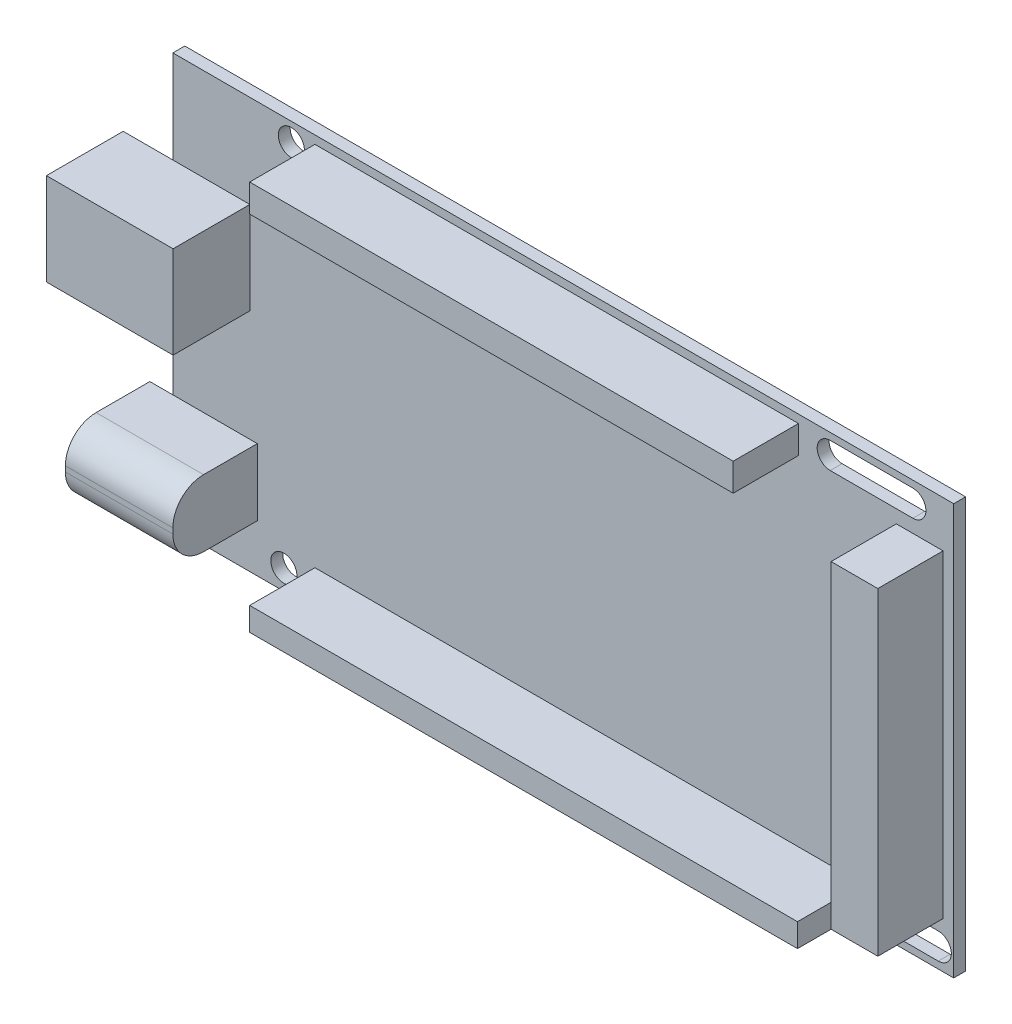
SolidWorks part; units mm, degrees
ref_plane "前视" through (0, 0, 0) normal (0, 0, 1) x (1, 0, 0)
ref_plane "上视" through (0, 0, 0) normal (0, 1, 0) x (1, 0, 0)
ref_plane "右视" through (0, 0, 0) normal (1, 0, 0) x (0, 0, -1)
sketch "草图1" plane through (0, 0, 0) normal (0, 0, 1) x (1, 0, 0)
  line L1 (-49.2002, 28.0388) -> (52.4998, 28.0388)
  line L2 (-49.2002, 28.0388) -> (-49.2002, -25.4612)
  line L3 (-49.2002, -25.4612) -> (52.4998, -25.4612)
  line L4 (52.4998, 28.0388) -> (52.4998, -25.4612)
extrude "凸台-拉伸1" add sketch "草图1" along normal blind 1.55
sketch "草图2" plane through (0, 0, 1.55) normal (0, 0, 1) x (1, 0, 0)
  line L0 (-49.2002, -25.4612) -> (52.4998, -25.4612) construction
  line L1 (-49.2002, 28.0388) -> (-49.2002, -25.4612) construction
  line L2 (52.4998, 28.0388) -> (-49.2002, 28.0388) construction
  line L3 (36.4187, 25.4388) -> (47.1808, 25.4388) construction
  line L4 (36.4187, 27.1388) -> (47.1808, 27.1388)
  line L5 (36.4187, 23.7388) -> (47.1808, 23.7388)
  line L6 (52.4998, -25.4612) -> (52.4998, 28.0388) construction
  line L7 (45.1092, -22.8612) -> (50.4903, -22.8612) construction
  line L8 (45.1092, -21.1612) -> (50.4903, -21.1612)
  line L9 (45.1092, -24.5612) -> (50.4903, -24.5612)
  circle A0 centre (-34.7402, -22.8612) radius 1.7
  circle A1 centre (-33.7702, 25.6388) radius 1.7
  arc A2 (36.4187, 27.1388) -> (36.4187, 23.7388) centre (36.4187, 25.4388) ccw
  arc A3 (47.1808, 23.7388) -> (47.1808, 27.1388) centre (47.1808, 25.4388) ccw
  arc A4 (45.1092, -21.1612) -> (45.1092, -24.5612) centre (45.1092, -22.8612) ccw
  arc A5 (50.4903, -24.5612) -> (50.4903, -21.1612) centre (50.4903, -22.8612) ccw
  point P12 (41.7998, 25.4388)
  point P21 (47.7998, -22.8612)
  dimension "D1" = 2.6
  dimension "D3" = 2.4
  dimension "D2" = 14.46
  dimension "D4" = 15.43
  dimension "D5" = 3.4
  dimension "D6" = 10.7622
  dimension "D7" = 2.6
  dimension "D8" = 10.7
  dimension "D9" = 3.4
  dimension "D10" = 5.3811
  dimension "D11" = 4.7
extrude "切除-拉伸1" cut sketch "草图2" against normal blind 1.55
sketch "草图3" plane through (0, 0, 1.55) normal (0, 0, 1) x (1, 0, 0)
  line L0 (-55.6702, 15.9569) -> (-55.6702, 3.9569)
  line L1 (-55.6702, 15.9569) -> (-39.1702, 15.9569)
  line L2 (-55.6702, 3.9569) -> (-39.1702, 3.9569)
  line L3 (-39.1702, 15.9569) -> (-39.1702, 3.9569)
  line L5 (-49.2002, 28.0388) -> (-49.2002, -25.4612) construction
  dimension "D1" = 12
  dimension "D2" = 16.5
  dimension "D3" = 6.47
extrude "凸台-拉伸2" add sketch "草图3" along normal blind 10
sketch "草图4" plane through (0, 0, 1.55) normal (0, 0, 1) x (1, 0, 0)
  line L0 (-52.2002, -10.5345) -> (-52.2002, -19.2345)
  line L1 (-52.2002, -10.5345) -> (-38.2002, -10.5345)
  line L2 (-52.2002, -19.2345) -> (-38.2002, -19.2345)
  line L3 (-38.2002, -10.5345) -> (-38.2002, -19.2345)
  line L4 (-49.2002, 3.9569) -> (-49.2002, -25.4612) construction
  dimension "D1" = 8.7
  dimension "D2" = 14
  dimension "D3" = 3
extrude "凸台-拉伸3" add sketch "草图4" along normal blind 11
fillet "圆角1" radius 4 2 edges at (-45.2002, -10.5345, 12.55) (-45.2002, -19.2345, 12.55)
sketch "草图5" plane through (-55.6702, 0, 0) normal (-1, 0, 0) x (0, 0, 1)
  line L0 (2.5693, 14.806) -> (10.9719, 14.806)
  line L1 (2.5693, 14.806) -> (2.5693, 5.1857)
  line L2 (10.9719, 14.806) -> (10.9719, 5.1857)
  line L3 (2.5693, 5.1857) -> (10.9719, 5.1857)
extrude "切除-拉伸3" cut sketch "草图5" against normal blind 12.6
sketch "草图6" plane through (-52.2002, 0, 0) normal (-1, 0, 0) x (0, 0, 1)
  circle A0 centre (8.55, -14.5345) radius 3.3
extrude "切除-拉伸4" cut sketch "草图6" against normal blind 12.6
sketch "草图7" plane through (0, 0, 1.55) normal (0, 0, 1) x (1, 0, 0)
  line L0 (-30.6947, 26.9737) -> (-30.6947, 23.3588)
  line L1 (-30.6947, 26.9737) -> (32.2807, 26.9737)
  line L2 (-30.6947, 23.3588) -> (32.2807, 23.3588)
  line L3 (32.2807, 26.9737) -> (32.2807, 23.3588)
  line L4 (45.028, 22.027) -> (51.1162, 22.027)
  line L5 (45.028, 22.027) -> (45.028, -19.4493)
  line L6 (51.1162, 22.027) -> (51.1162, -19.4493)
  line L7 (45.028, -19.4493) -> (51.1162, -19.4493)
  line L8 (-30.6947, -20.7811) -> (-30.6947, -23.8252)
  line L9 (-30.6947, -20.7811) -> (40.652, -20.7811)
  line L10 (-30.6947, -23.8252) -> (40.652, -23.8252)
  line L11 (40.652, -20.7811) -> (40.652, -23.8252)
extrude "凸台-拉伸4" add sketch "草图7" along normal blind 8.5
